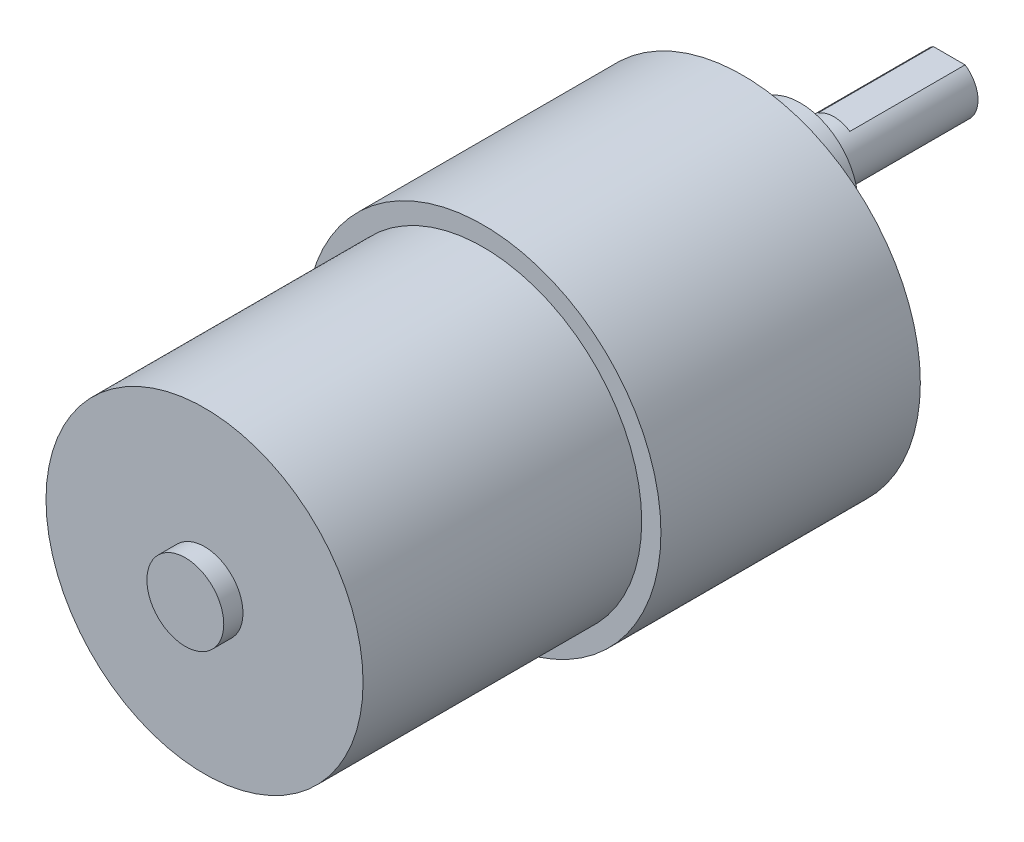
SolidWorks part; units mm, degrees
ref_plane "Front Plane" through (0, 0, 0) normal (0, 0, 1) x (1, 0, 0)
ref_plane "Top Plane" through (0, 0, 0) normal (0, 1, 0) x (1, 0, 0)
ref_plane "Right Plane" through (0, 0, 0) normal (1, 0, 0) x (0, 0, -1)
sketch "Sketch1" plane through (0, 0, 0) normal (0, 0, 1) x (1, 0, 0)
  circle A0 centre (0, 0) radius 18.5
  dimension "D1" = 37
extrude "Boss-Extrude1" add sketch "Sketch1" along normal blind 27
sketch "Sketch2" plane through (0, 0, 27) normal (0, 0, 1) x (1, 0, 0)
  circle A0 centre (0, 0) radius 16.5
  dimension "D1" = 33
extrude "Boss-Extrude2" add sketch "Sketch2" along normal blind 29
sketch "Sketch3" plane through (0, 0, 56) normal (0, 0, 1) x (1, 0, 0)
  circle A0 centre (0, 0) radius 4
  dimension "D1" = 8
extrude "Boss-Extrude3" add sketch "Sketch3" along normal blind 2
sketch "Sketch4" plane through (0, 0, 0) normal (0, 0, -1) x (-1, 0, 0)
  line L0 (0, 0) -> (0, -1.1387) construction
  line L1 (-18.4988, -0.2134) -> (18.4988, 0.2134) construction
  line L2 (0, 18.5) -> (0, -18.5) construction
  circle A0 centre (0, 0) radius 18.5 construction
  circle A1 centre (0, 7.0005) radius 6
  circle A2 centre (-15.5, -0.1788) radius 0.5
  circle A4 centre (-7.9048, 13.334) radius 0.5
  circle A5 centre (7.5952, 13.5128) radius 0.5
  circle A6 centre (15.5, 0.1788) radius 0.5
  circle A7 centre (7.9048, -13.334) radius 0.5
  circle A8 centre (-7.5952, -13.5128) radius 0.5
  point P27 (0, 0)
  dimension "D2" = 12
  dimension "D5" = 1
  dimension "D1" = 7
  dimension "D3" = 15.5
  dimension "D4" = 6
hole_wizard "M3 Tapped Hole1" positions "3DSketch1" profile "Sketch5" tap size "M3" standard "ISO"
sketch3d "3DSketch1"
  point P0 (15.5, -0.1788, 0)
  point P3 (7.9048, 13.334, 0)
  point P6 (-7.5952, 13.5128, 0)
  point P9 (-15.5, 0.1788, 0)
  point P12 (-7.9048, -13.334, 0)
  point P15 (7.5952, -13.5128, 0)
sketch "Sketch5" plane through (15.5, -0.1788, 0) normal (1, 0, 0) x (0, 1, 0)
  line L0 (0, 0) -> (0, 9.2511)
  line L1 (0, 9.2511) -> (1.25, 8.5)
  line L2 (1.25, 8.5) -> (1.25, 0)
  line L5 (1.25, 0) -> (0, 0)
  line L10 (0, 9.2511) -> (-1.25, 8.5) construction
  line L11 (0, -6.35) -> (0, 107.95) construction
  dimension "Tap Drill Dia." = 2.5
  dimension "Tap Drill Depth" = 8.5
  dimension "Drill Angle" = 118
cosmetic thread "Hole Thread1" parameters "D1"=6, "D2"=3
cosmetic thread "Hole Thread2" parameters "D1"=6, "D2"=3
cosmetic thread "Hole Thread3" parameters "D1"=6, "D2"=3
cosmetic thread "Hole Thread4" parameters "D1"=6, "D2"=3
cosmetic thread "Hole Thread5" parameters "D1"=6, "D2"=3
cosmetic thread "Hole Thread6" parameters "D1"=6, "D2"=3
extrude "Boss-Extrude4" add sketch "Sketch4" along normal blind 6 contours A1
sketch "Sketch7" plane through (0, 0, -6) normal (0, 0, -1) x (-1, 0, 0)
  circle A0 centre (0, 7.0005) radius 3
  dimension "D1" = 6
extrude "Boss-Extrude5" add sketch "Sketch7" along normal blind 15.5
sketch "Sketch8" plane through (0, 0, -21.5) normal (0, 0, -1) x (-1, 0, 0)
  line L0 (-1.6583, 9.5005) -> (1.6583, 9.5005)
  circle A0 centre (0, 7.0005) radius 3 construction
  circle M2 centre (0, 7.0005) radius 3
  dimension "D1" = 2.5
extrude "Cut-Extrude1" cut sketch "Sketch8" against normal blind 12 and the other way through all contours L0 M2
